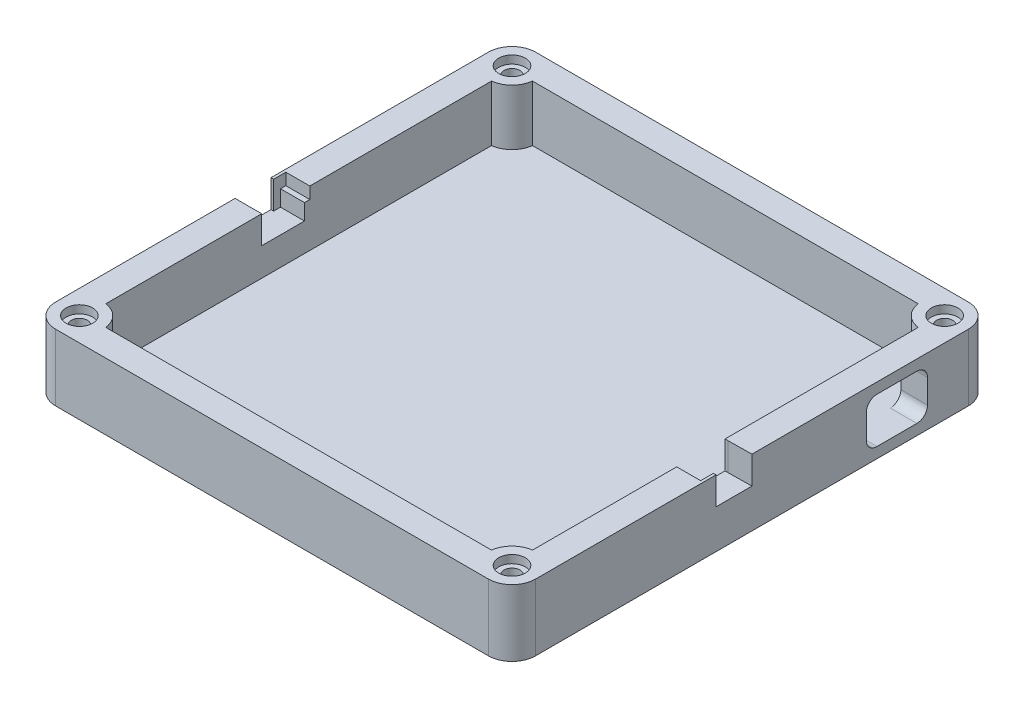
SolidWorks part; units mm, degrees
ref_plane "Front Plane" through (0, 0, 0) normal (0, 0, 1) x (1, 0, 0)
ref_plane "Top Plane" through (0, 0, 0) normal (0, 1, 0) x (1, 0, 0)
ref_plane "Right Plane" through (0, 0, 0) normal (1, 0, 0) x (0, 0, -1)
sketch "Sketch1" plane through (0, 0, 0) normal (0, 1, 0) x (1, 0, 0)
  line L0 (0, 0) -> (0, 40.64)
  line L1 (0, 40.64) -> (40.64, 40.64)
  line L2 (40.64, 40.64) -> (40.64, -40.64)
  line L3 (40.64, -40.64) -> (-40.64, -40.64)
  line L4 (-40.64, -40.64) -> (-40.64, 40.64)
  line L5 (-40.64, 40.64) -> (0, 40.64)
  line L6 (-40.64, -45.0809) -> (40.64, -45.0809)
  line L7 (-45.0809, -40.64) -> (-45.0809, 40.64)
  line L8 (-40.64, 45.0809) -> (40.64, 45.0809)
  line L9 (45.0809, 40.64) -> (45.0809, -40.64)
  line L10 (-45.0809, 18.4234) -> (-40.0809, 18.4234)
  line L11 (-7.938, 45.0809) -> (-7.938, 40.0809)
  line L12 (45.0809, 28.2685) -> (40.0809, 28.2685)
  line L13 (27.0858, -45.0809) -> (27.0858, -40.0809)
  line L14 (27.0858, -40.0809) -> (36.2345, -40.0809)
  line L15 (36.2345, -40.0809) -> (-36.2345, -40.0809)
  line L16 (-40.0809, 18.4234) -> (-40.0809, 36.2345)
  line L17 (-40.0809, 36.2345) -> (-40.0809, -36.2345)
  line L18 (-7.938, 40.0809) -> (-36.2345, 40.0809)
  line L19 (-36.2345, 40.0809) -> (36.2345, 40.0809)
  line L20 (40.0809, 28.2685) -> (40.0809, 36.2345)
  line L21 (40.0809, 36.2345) -> (40.0809, -36.2345)
  arc A0 (40.64, 45.0809) -> (45.0809, 40.64) centre (40.64, 40.64) cw
  arc A1 (-40.64, 45.0809) -> (-45.0809, 40.64) centre (-40.64, 40.64) ccw
  arc A2 (-45.0809, -40.64) -> (-40.64, -45.0809) centre (-40.64, -40.64) ccw
  arc A3 (45.0809, -40.64) -> (40.64, -45.0809) centre (40.64, -40.64) cw
  circle A4 centre (40.64, 40.64) radius 4.4409
  circle A5 centre (-40.64, 40.64) radius 4.4409
  circle A6 centre (-40.64, -40.64) radius 4.4409
  circle A7 centre (40.64, -40.64) radius 4.4409
extrude "Boss-Extrude1" add sketch "Sketch1" along normal blind 11.5 contours A6 L17 L10 L4 | A5 L4 L10 L16 | A5 L18 L11 L5 | A4 L1 L0 L19 | L11 L19 L0 L5 | A4 L20 L12 L2 | A7 L2 L12 L21 | L2 A7 L3 | A7 L14 L13 L3 | A6 L3 L13 L15 | A2 A6 L3 L4 | L3 A6 L4 | A6 L6 L13 L3 | A6 L4 L10 L7 | A3 A7 L2 L3 | A7 L3 L13 L6 | A7 L9 L12 L2 | A4 L2 L12 L9 | L2 A4 A0 L1 | L1 A4 L2 | A4 L8 L11 L5 L1 | A5 L5 L11 L8 | L5 A5 A1 L4 | L4 A5 L5 | A5 L7 L10 L4
sketch "Sketch2" plane through (0, 11.5, 0) normal (0, 1, 0) x (1, 0, 0)
  circle A0 centre (-40.64, 40.64) radius 1.5
  circle A1 centre (40.64, 40.64) radius 1.5
  circle A3 centre (40.64, -40.64) radius 1.5
  circle A4 centre (-40.64, -40.64) radius 1.5
extrude "Cut-Extrude1" cut sketch "Sketch2" against normal blind 8
sketch "Sketch3" plane through (45.0809, 0, 0) normal (1, 0, 0) x (0, 0, -1)
  line L0 (40.64, 11.5) -> (40.64, 0) construction
  line L1 (40.64, 11.5) -> (40.64, 0)
  line L2 (40.64, 11.5) -> (27.229, 11.5)
  line L3 (40.64, 11.5) -> (-40.64, 11.5) construction
  line L4 (27.229, 11.5) -> (27.229, 9.5)
  line L5 (28.6092, 11.5) -> (28.6092, 1)
  line L6 (27.229, 9.5) -> (32.979, 9.5)
  line L7 (32.979, 9.5) -> (32.979, 1)
  line L8 (32.979, 1) -> (27.229, 1)
  line L9 (27.229, 1) -> (21.479, 1)
  line L10 (21.479, 1) -> (21.479, 9.5)
  line L11 (21.479, 9.5) -> (27.229, 9.5)
  line L12 (32.979, 9.5) -> (32.979, 7.5)
  line L13 (32.979, 7.5) -> (30.979, 7.5)
  line L14 (32.979, 1) -> (32.979, 3)
  line L15 (32.979, 3) -> (30.979, 3)
  line L16 (21.479, 1) -> (23.479, 1)
  line L17 (23.479, 1) -> (23.479, 3)
  line L18 (21.479, 9.5) -> (23.479, 9.5)
  line L19 (23.479, 9.5) -> (23.479, 7.5)
  arc A0 (32.979, 7.5) -> (30.979, 9.5) centre (30.979, 7.5) ccw
  arc A1 (32.979, 3) -> (30.979, 1) centre (30.979, 3) cw
  arc A2 (23.479, 1) -> (21.479, 3) centre (23.479, 3) cw
  arc A3 (23.479, 9.5) -> (21.479, 7.5) centre (23.479, 7.5) ccw
extrude "Cut-Extrude2" cut sketch "Sketch3" against normal blind 8
sketch "Sketch4" plane through (0, 11.5, 0) normal (0, 1, 0) x (1, 0, 0)
  circle A0 centre (-40.64, 40.64) radius 2.5
  circle A1 centre (40.64, 40.64) radius 2.5
  circle A2 centre (40.64, -40.64) radius 2.5
  circle A3 centre (-40.64, -40.64) radius 2.5
extrude "Cut-Extrude3" cut sketch "Sketch4" against normal blind 1.5
sketch "Sketch5" plane through (0, 0, 0) normal (0, -1, 0) x (1, 0, 0)
  line L0 (36.2345, -40.0809) -> (-36.2345, -40.0809) construction
  line L1 (40.0809, 36.2345) -> (40.0809, -36.2345) construction
  line L2 (36.2345, 40.0809) -> (-36.2345, 40.0809) construction
  line L3 (-40.0809, 36.2345) -> (-40.0809, -36.2345) construction
  line L4 (40.64, 45.0809) -> (-40.64, 45.0809)
  line L5 (-45.0809, 40.64) -> (-45.0809, -40.64)
  line L6 (-40.64, -45.0809) -> (40.64, -45.0809)
  line L7 (45.0809, -40.64) -> (45.0809, 40.64)
  line L8 (40.64, 45.0809) -> (-40.64, 45.0809)
  line L9 (-45.0809, 40.64) -> (-45.0809, -40.64)
  line L10 (-40.64, -45.0809) -> (40.64, -45.0809)
  line L11 (45.0809, -40.64) -> (45.0809, 40.64)
  line L12 (36.2345, -40.0809) -> (-36.2345, -40.0809)
  line L13 (40.0809, 36.2345) -> (40.0809, -36.2345)
  line L14 (36.2345, 40.0809) -> (-36.2345, 40.0809)
  line L15 (-40.0809, 36.2345) -> (-40.0809, -36.2345)
  arc A0 (40.0809, -36.2345) -> (36.2345, -40.0809) centre (40.64, -40.64) ccw construction
  arc A1 (36.2345, 40.0809) -> (40.0809, 36.2345) centre (40.64, 40.64) ccw construction
  arc A2 (-40.0809, 36.2345) -> (-36.2345, 40.0809) centre (-40.64, 40.64) ccw construction
  arc A3 (40.0809, -36.2345) -> (36.2345, -40.0809) centre (40.64, -40.64) ccw
  arc A4 (-40.64, 45.0809) -> (-45.0809, 40.64) centre (-40.64, 40.64) ccw
  arc A5 (-45.0809, -40.64) -> (-40.64, -45.0809) centre (-40.64, -40.64) ccw
  arc A6 (40.64, -45.0809) -> (45.0809, -40.64) centre (40.64, -40.64) ccw
  arc A7 (45.0809, 40.64) -> (40.64, 45.0809) centre (40.64, 40.64) ccw
  arc A8 (-40.64, 45.0809) -> (-45.0809, 40.64) centre (-40.64, 40.64) ccw
  arc A9 (-45.0809, -40.64) -> (-40.64, -45.0809) centre (-40.64, -40.64) ccw
  arc A10 (40.64, -45.0809) -> (45.0809, -40.64) centre (40.64, -40.64) ccw
  arc A11 (45.0809, 40.64) -> (40.64, 45.0809) centre (40.64, 40.64) ccw
  arc A12 (36.2345, 40.0809) -> (40.0809, 36.2345) centre (40.64, 40.64) ccw
  arc A13 (-40.0809, 36.2345) -> (-36.2345, 40.0809) centre (-40.64, 40.64) ccw
  arc M9 (36.2345, 40.0809) -> (40.0809, 36.2345) centre (40.64, 40.64) ccw
  line M10 (40.0809, 36.2345) -> (40.0809, -36.2345)
  arc M11 (40.0809, -36.2345) -> (36.2345, -40.0809) centre (40.64, -40.64) ccw
  line M12 (36.2345, -40.0809) -> (-36.2345, -40.0809)
  arc M13 (-36.2345, -40.0809) -> (-40.0809, -36.2345) centre (-40.64, -40.64) ccw
  line M14 (-40.0809, -36.2345) -> (-40.0809, 36.2345)
  arc M15 (-40.0809, 36.2345) -> (-36.2345, 40.0809) centre (-40.64, 40.64) ccw
  line M16 (-36.2345, 40.0809) -> (36.2345, 40.0809)
  dimension "D1" = 0
extrude "Boss-Extrude2" add sketch "Sketch5" against normal up to surface (1 mm away) contours M9 M16 M15 M14 M13 M12 M11 M10 up to face at (42.5809, 1, -27.229)
sketch "Sketch6" plane through (0, 0, 0) normal (0, -1, 0) x (1, 0, 0)
  line L4 (40.64, 45.0809) -> (-40.64, 45.0809)
  line L5 (-45.0809, 40.64) -> (-45.0809, -40.64)
  line L6 (-40.64, -45.0809) -> (40.64, -45.0809)
  line L7 (45.0809, -40.64) -> (45.0809, 40.64)
  line L8 (40.64, 45.0809) -> (-40.64, 45.0809)
  line L9 (-45.0809, 40.64) -> (-45.0809, -40.64)
  line L10 (-40.64, -45.0809) -> (40.64, -45.0809)
  line L11 (45.0809, -40.64) -> (45.0809, 40.64)
  arc A4 (-40.64, 45.0809) -> (-45.0809, 40.64) centre (-40.64, 40.64) ccw
  arc A5 (-45.0809, -40.64) -> (-40.64, -45.0809) centre (-40.64, -40.64) ccw
  arc A6 (40.64, -45.0809) -> (45.0809, -40.64) centre (40.64, -40.64) ccw
  arc A7 (45.0809, 40.64) -> (40.64, 45.0809) centre (40.64, 40.64) ccw
  arc A8 (-40.64, 45.0809) -> (-45.0809, 40.64) centre (-40.64, 40.64) ccw
  arc A9 (-45.0809, -40.64) -> (-40.64, -45.0809) centre (-40.64, -40.64) ccw
  arc A10 (40.64, -45.0809) -> (45.0809, -40.64) centre (40.64, -40.64) ccw
  arc A11 (45.0809, 40.64) -> (40.64, 45.0809) centre (40.64, 40.64) ccw
  dimension "D1" = 0
extrude "Boss-Extrude3" add sketch "Sketch6" along normal blind 1
sketch "Sketch7" plane through (0, -1, 0) normal (0, -1, 0) x (1, 0, 0)
  circle A8 centre (-40.64, 40.64) radius 2.75
  circle A9 centre (40.64, 40.64) radius 2.75
  circle A10 centre (40.64, -40.64) radius 2.75
  circle A11 centre (-40.64, -40.64) radius 2.75
extrude "Cut-Extrude4" cut sketch "Sketch7" against normal blind 1
sketch "Sketch8" plane through (0, 11.5, 0) normal (0, 1, 0) x (1, 0, 0)
  line L0 (40.64, -40.64) -> (40.64, -9.14)
  line L1 (40.64, -9.14) -> (40.0809, -9.14)
  line L2 (40.0809, -36.2345) -> (40.0809, 36.2345) construction
  line L3 (40.64, -9.14) -> (45.0809, -9.14)
  line L4 (45.0809, 40.64) -> (45.0809, -40.64) construction
  line L5 (40.64, 40.64) -> (40.64, -0.06)
  line L6 (40.64, -0.06) -> (45.0809, 0)
  line L7 (45.0809, 0) -> (45.0809, -9.14)
  line L8 (40.64, -0.06) -> (40.0809, -0.06)
  line L9 (40.0809, -0.06) -> (40.0809, -9.14)
  line L10 (-40.64, -40.64) -> (-40.64, -6.94)
  line L11 (-40.64, 40.64) -> (-40.64, 2.09)
  line L12 (-40.64, 2.09) -> (-45.0809, 2.09)
  line L13 (-45.0809, -40.64) -> (-45.0809, 40.64) construction
  line L14 (-45.0809, 2.09) -> (-45.0809, -6.94)
  line L15 (-45.0809, -6.94) -> (-40.0809, -6.94)
  line L16 (-40.0809, -36.2345) -> (-40.0809, 36.2345) construction
  line L17 (-40.0809, -6.94) -> (-40.0809, 2.09)
  line L18 (-40.0809, 2.09) -> (-40.64, 2.09)
  line L19 (40.64, -40.64) -> (40.64, -6.74)
  line L20 (40.64, -6.74) -> (45.0809, -6.74)
  line L21 (45.0809, -6.74) -> (40.0809, -6.74)
  line L22 (-40.64, 40.64) -> (-40.64, -0.19)
  line L23 (-40.64, -0.19) -> (-40.0809, -0.19)
  line L24 (-40.0809, -0.19) -> (-45.0809, -0.19)
  line L25 (-45.0809, 2.09) -> (-44.3809, 2.09)
  line L26 (-45.0809, 2.09) -> (-44.5809, 2.09)
  line L27 (45.0809, -9.14) -> (44.3809, -9.14)
  line L28 (45.0809, -9.14) -> (44.5809, -9.14)
  line L29 (44.5809, -9.14) -> (44.5809, -6.74)
  line L30 (-44.5809, 2.09) -> (-44.5809, -0.19)
extrude "Cut-Extrude5" cut sketch "Sketch8" against normal blind 5.2
sketch "Sketch9" plane through (0, 6.3, 0) normal (0, 1, 0) x (1, 0, 0)
  line L0 (-40.0809, 2.09) -> (-40.0809, 1.09)
  line L1 (-40.0809, -6.94) -> (-40.0809, 2.09) construction
  line L2 (-40.0809, 1.09) -> (-44.5809, 1.09)
  line L3 (40.0809, -9.14) -> (40.0809, -8.14)
  line L4 (40.0809, -0.06) -> (40.0809, -9.14) construction
  line L5 (40.0809, -8.14) -> (44.5809, -8.14)
  line L10 (-40.0809, -6.94) -> (-45.0809, -6.94)
  line L11 (-44.5809, 2.09) -> (-40.0809, 2.09)
  line L12 (-40.0809, 2.09) -> (-40.0809, 36.2345)
  line L13 (-36.2345, 40.0809) -> (36.2345, 40.0809)
  line L14 (40.0809, 36.2345) -> (40.0809, -0.06)
  line L15 (40.0809, -0.06) -> (40.64, -0.06)
  line L16 (40.64, -0.06) -> (45.0809, 0)
  line L17 (45.0809, 0) -> (45.0809, 40.64)
  line L18 (40.64, 45.0809) -> (-40.64, 45.0809)
  line L19 (-45.0809, 40.64) -> (-45.0809, -0.19)
  line L20 (-45.0809, -0.19) -> (-44.5809, -0.19)
  line L21 (-44.5809, -0.19) -> (-44.5809, 2.09)
  line L22 (-44.5809, 2.09) -> (-40.0809, 2.09)
  line L23 (-40.0809, 2.09) -> (-40.0809, 36.2345)
  line L24 (-36.2345, 40.0809) -> (36.2345, 40.0809)
  line L25 (40.0809, 36.2345) -> (40.0809, -0.06)
  line L26 (40.0809, -0.06) -> (40.64, -0.06)
  line L27 (40.64, -0.06) -> (45.0809, 0)
  line L28 (45.0809, 0) -> (45.0809, 40.64)
  line L29 (40.64, 45.0809) -> (-40.64, 45.0809)
  line L30 (-45.0809, 40.64) -> (-45.0809, -0.19)
  line L31 (-45.0809, -0.19) -> (-44.5809, -0.19)
  line L32 (-44.5809, -0.19) -> (-44.5809, 2.09)
  line L33 (-45.0809, -6.94) -> (-45.0809, -40.64)
  line L34 (-40.64, -45.0809) -> (40.64, -45.0809)
  line L35 (45.0809, -40.64) -> (45.0809, -6.74)
  line L36 (45.0809, -6.74) -> (44.5809, -6.74)
  line L37 (44.5809, -6.74) -> (44.5809, -9.14)
  line L38 (44.5809, -9.14) -> (40.0809, -9.14)
  line L39 (40.0809, -9.14) -> (40.0809, -36.2345)
  line L40 (36.2345, -40.0809) -> (-36.2345, -40.0809)
  line L41 (-40.0809, -36.2345) -> (-40.0809, -6.94)
  line L42 (-40.0809, -6.94) -> (-45.0809, -6.94)
  line L43 (-45.0809, -6.94) -> (-45.0809, -40.64)
  line L44 (-40.64, -45.0809) -> (40.64, -45.0809)
  line L45 (45.0809, -40.64) -> (45.0809, -6.74)
  line L46 (45.0809, -6.74) -> (44.5809, -6.74)
  line L47 (44.5809, -6.74) -> (44.5809, -9.14)
  line L48 (44.5809, -9.14) -> (40.0809, -9.14)
  line L49 (40.0809, -9.14) -> (40.0809, -36.2345)
  line L50 (36.2345, -40.0809) -> (-36.2345, -40.0809)
  line L51 (-40.0809, -36.2345) -> (-40.0809, -6.94)
  arc A4 (-40.0809, 36.2345) -> (-36.2345, 40.0809) centre (-40.64, 40.64) ccw
  arc A5 (36.2345, 40.0809) -> (40.0809, 36.2345) centre (40.64, 40.64) ccw
  arc A6 (45.0809, 40.64) -> (40.64, 45.0809) centre (40.64, 40.64) ccw
  arc A7 (-40.64, 45.0809) -> (-45.0809, 40.64) centre (-40.64, 40.64) ccw
  arc A8 (-40.0809, 36.2345) -> (-36.2345, 40.0809) centre (-40.64, 40.64) ccw
  arc A9 (36.2345, 40.0809) -> (40.0809, 36.2345) centre (40.64, 40.64) ccw
  arc A10 (45.0809, 40.64) -> (40.64, 45.0809) centre (40.64, 40.64) ccw
  arc A11 (-40.64, 45.0809) -> (-45.0809, 40.64) centre (-40.64, 40.64) ccw
  arc A12 (-45.0809, -40.64) -> (-40.64, -45.0809) centre (-40.64, -40.64) ccw
  arc A13 (40.64, -45.0809) -> (45.0809, -40.64) centre (40.64, -40.64) ccw
  arc A14 (40.0809, -36.2345) -> (36.2345, -40.0809) centre (40.64, -40.64) ccw
  arc A15 (-36.2345, -40.0809) -> (-40.0809, -36.2345) centre (-40.64, -40.64) ccw
  arc A16 (-45.0809, -40.64) -> (-40.64, -45.0809) centre (-40.64, -40.64) ccw
  arc A17 (40.64, -45.0809) -> (45.0809, -40.64) centre (40.64, -40.64) ccw
  arc A18 (40.0809, -36.2345) -> (36.2345, -40.0809) centre (40.64, -40.64) ccw
  arc A19 (-36.2345, -40.0809) -> (-40.0809, -36.2345) centre (-40.64, -40.64) ccw
  line M30 (-40.0809, 2.09) -> (-44.5809, 2.09)
  line M31 (-44.5809, 2.09) -> (-44.5809, -0.19)
  line M35 (-40.0809, -6.94) -> (-40.0809, 2.09)
  dimension "D1" = 0
  dimension "D2" = 0
extrude "Boss-Extrude4" add sketch "Sketch9" along normal blind 3 contours L48 L47 L5 L3 | L2 M35 M30 M31
